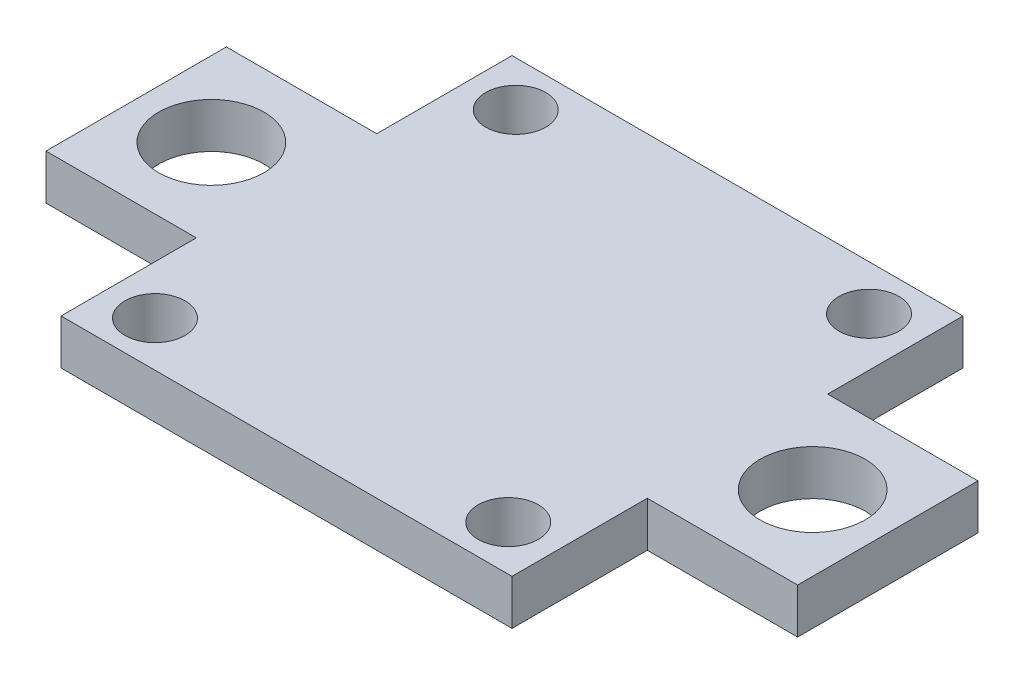
SolidWorks part; units mm, degrees
ref_plane "Front Plane" through (0, 0, 0) normal (0, 0, 1) x (1, 0, 0)
ref_plane "Top Plane" through (0, 0, 0) normal (0, 1, 0) x (1, 0, 0)
ref_plane "Right Plane" through (0, 0, 0) normal (1, 0, 0) x (0, 0, -1)
sketch "Sketch1" plane through (0, 0, 0) normal (0, 1, 0) x (1, 0, 0)
  line L0 (-15, -6) -> (-15, -15)
  line L1 (-15, 15) -> (15, 15)
  line L2 (-15, 15) -> (-15, 6)
  line L3 (-15, -15) -> (15, -15)
  line L4 (15, 15) -> (15, 6)
  line L5 (-25, 6) -> (-15, 6)
  line L6 (-25, 6) -> (-25, -6)
  line L7 (-25, -6) -> (-15, -6)
  line L8 (25, 6) -> (25, -6)
  line L9 (15, 6) -> (25, 6)
  line L10 (15, -6) -> (25, -6)
  line L11 (15, -6) -> (15, -15)
  point P8 (0, -15)
  point P11 (25, 0)
  point P18 (-25, 0)
  point P20 (0, 15)
  dimension "D1" = 30
  dimension "D2" = 12
  dimension "D3" = 50
  dimension "D4" = 30
extrude "Boss-Extrude1" add sketch "Sketch1" along normal blind 3
sketch "Sketch2" plane through (0, 3, 0) normal (0, 1, 0) x (1, 0, 0)
  line L0 (0, 15) -> (0, -15) construction
  line L1 (15, 15) -> (-15, 15) construction
  line L2 (-15, -15) -> (15, -15) construction
  line L3 (-15, 6) -> (-25, 6) construction
  line L4 (-11.75, 12) -> (-11.75, 15) construction
  line L5 (-11.75, -12) -> (-11.75, -15) construction
  circle A0 centre (-20, 0) radius 3.5
  circle A1 centre (-11.75, 12) radius 2
  circle A2 centre (-11.75, -12) radius 2
  circle A3 centre (11.75, -12) radius 2
  circle A4 centre (20, 0) radius 3.5
  circle A5 centre (11.75, 12) radius 2
  point P18 (-20, 6)
  dimension "D1" = 7
  dimension "D2" = 4
  dimension "D4" = 24
  dimension "D5" = 11.75
  dimension "D6" = 11.75
extrude "Cut-Extrude1" cut sketch "Sketch2" against normal through all
equation "\"hole\"=4"
equation "\"D2@Sketch2\"=\"hole\""
